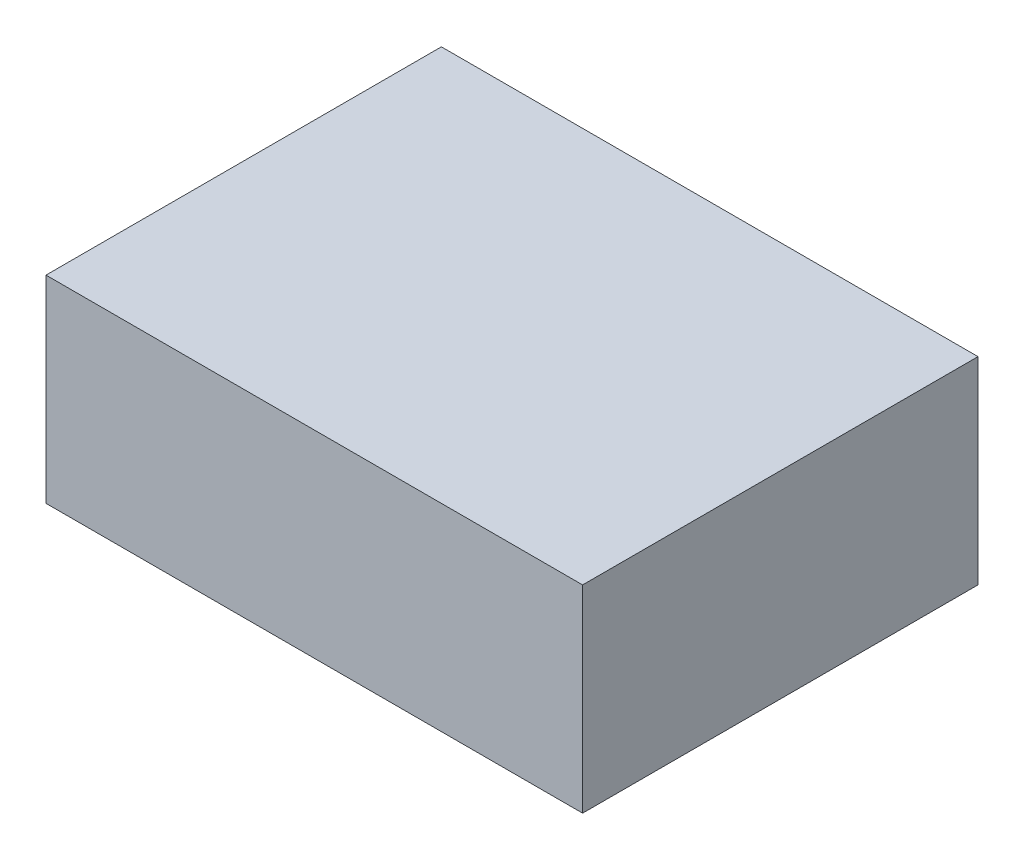
SolidWorks part; units mm, degrees
ref_plane "Front Plane" through (0, 0, 0) normal (0, 0, 1) x (1, 0, 0)
ref_plane "Top Plane" through (0, 0, 0) normal (0, 1, 0) x (1, 0, 0)
ref_plane "Right Plane" through (0, 0, 0) normal (1, 0, 0) x (0, 0, -1)
sketch "Sketch1" plane through (0, 0, 0) normal (0, 1, 0) x (1, 0, 0)
  line L1 (-47.5, 35) -> (47.5, 35)
  line L2 (-47.5, 35) -> (-47.5, -35)
  line L3 (-47.5, -35) -> (47.5, -35)
  line L4 (47.5, 35) -> (47.5, -35)
  line L5 (-47.5, 35) -> (47.5, -35) construction
  line L6 (-47.5, -35) -> (47.5, 35) construction
  point P0 (0, 0)
extrude "Boss-Extrude1" add sketch "Sketch1" along normal blind 35
